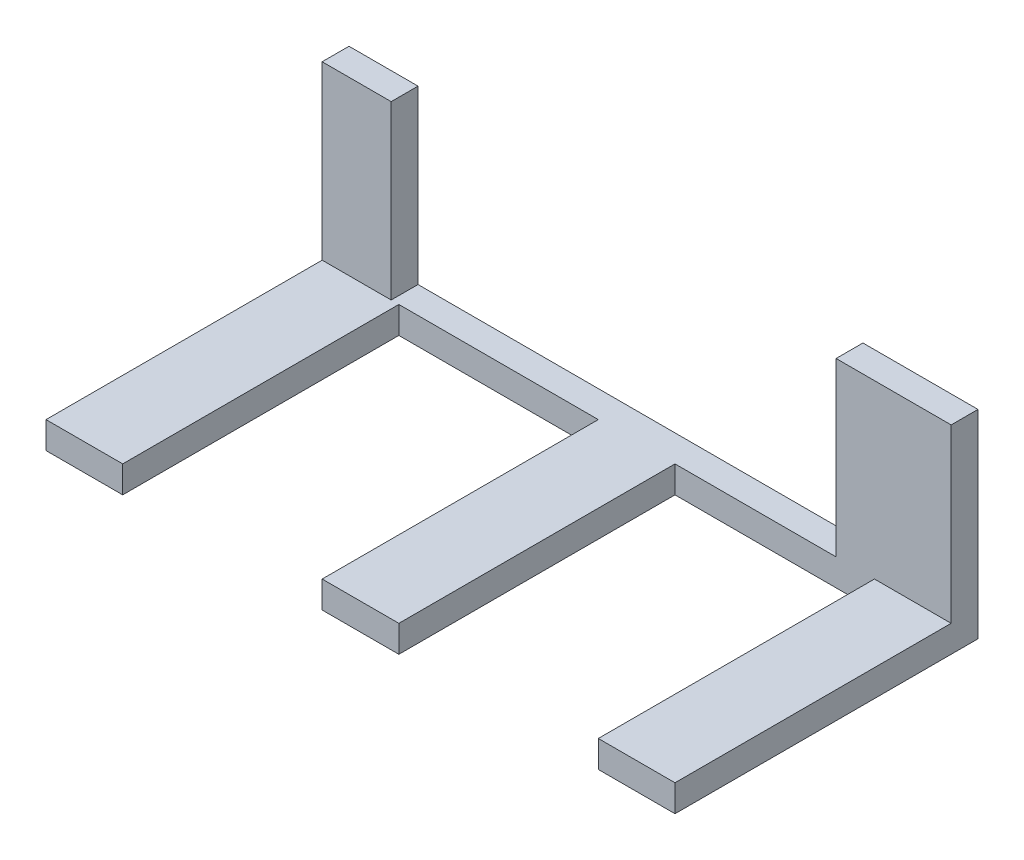
SolidWorks part; units mm, degrees
ref_plane "Alzado" through (0, 0, 0) normal (0, 0, 1) x (1, 0, 0)
ref_plane "Planta" through (0, 0, 0) normal (0, 1, 0) x (1, 0, 0)
ref_plane "Vista lateral" through (0, 0, 0) normal (1, 0, 0) x (0, 0, -1)
sketch "Croquis1" plane through (0, 0, 0) normal (0, 0, 1) x (1, 0, 0)
  line L0 (-58.7725, -24.9519) -> (23.2275, -24.9519)
  line L1 (-58.7725, -24.9519) -> (-58.7725, -28.4519)
  line L2 (-58.7725, -28.4519) -> (23.2275, -28.4519)
  line L3 (23.2275, -28.4519) -> (23.2275, -24.9519)
extrude "Saliente-Extruir1" add sketch "Croquis1" along normal blind 3.5
sketch "Croquis2" plane through (0, -24.9519, 0) normal (0, 1, 0) x (1, 0, 0)
  line L0 (23.2275, 0) -> (8.2275, 0)
  line L1 (23.2275, 0) -> (-58.7725, 0) construction
  line L2 (23.2275, -3.5) -> (23.2275, 0) construction
  line L3 (8.2275, 0) -> (8.2275, -3.5)
  line L4 (23.2275, -3.5) -> (-58.7725, -3.5) construction
  line L5 (8.2275, -3.5) -> (23.2275, -3.5)
  line L6 (23.2275, -3.5) -> (23.2275, 0)
  line L7 (-58.7725, 0) -> (-49.7725, 0)
  line L8 (-58.7725, -3.5) -> (-58.7725, 0) construction
  line L9 (-49.7725, 0) -> (-49.7725, -3.5)
  line L10 (-49.7725, -3.5) -> (-58.7725, -3.5)
  line L11 (-58.7725, -3.5) -> (-58.7725, 0)
extrude "Saliente-Extruir2" add sketch "Croquis2" along normal blind 22.4
sketch "Croquis3" plane through (0, 0, 3.5) normal (0, 0, 1) x (1, 0, 0)
  line L0 (-58.7725, -28.4519) -> (-48.7725, -28.4519)
  line L1 (-58.7725, -28.4519) -> (23.2275, -28.4519) construction
  line L4 (-58.7725, -2.5519) -> (-58.7725, -28.4519) construction
  line L5 (23.2275, -28.4519) -> (23.2275, -2.5519) construction
  line L6 (23.2275, -24.9519) -> (23.2275, -28.4519)
  line L7 (23.2275, -24.9519) -> (13.2275, -24.9519)
  line L8 (13.2275, -24.9519) -> (13.2275, -28.4519)
  line L9 (13.2275, -28.4519) -> (23.2275, -28.4519)
  line L10 (23.2275, -28.4519) -> (23.0562, -28.3651)
  line L11 (-48.7725, -28.4519) -> (-48.7725, -24.9519)
  line L12 (8.2275, -24.9519) -> (-49.7725, -24.9519) construction
  line L13 (-48.7725, -24.9519) -> (-58.7725, -24.9519)
  line L14 (-58.7725, -24.9519) -> (-58.7725, -28.4519)
  line L15 (-58.7725, -28.4519) -> (-22.7725, -28.4519)
  line L16 (-12.7725, -24.9519) -> (-22.7725, -24.9519)
  line L19 (-12.7725, -24.9519) -> (-12.7725, -28.4519)
  line L20 (-12.7725, -28.4519) -> (-22.7725, -28.4519)
  line L21 (-22.7725, -28.4519) -> (-22.7725, -24.9519)
extrude "Saliente-Extruir3" add sketch "Croquis3" along normal blind 36
